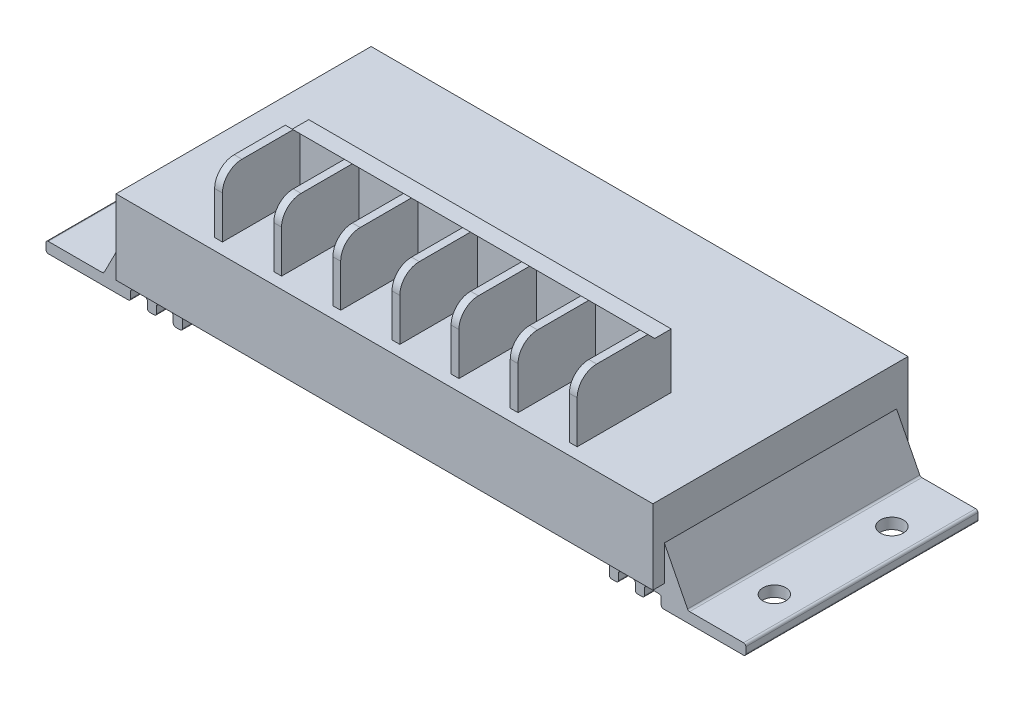
SolidWorks part; units mm, degrees
ref_plane "Front Plane" through (0, 0, 0) normal (0, 0, 1) x (1, 0, 0)
ref_plane "Top Plane" through (0, 0, 0) normal (0, 1, 0) x (1, 0, 0)
ref_plane "Right Plane" through (0, 0, 0) normal (1, 0, 0) x (0, 0, -1)
sketch "Sketch1" plane through (0, 0, 0) normal (0, 1, 0) x (1, 0, 0)
  line L1 (58.5, -27.8) -> (-58.5, -27.8)
  line L2 (58.5, -27.8) -> (58.5, 27.8)
  line L3 (58.5, 27.8) -> (-58.5, 27.8)
  line L4 (-58.5, -27.8) -> (-58.5, 27.8)
  line L5 (58.5, -27.8) -> (-58.5, 27.8) construction
  line L6 (58.5, 27.8) -> (-58.5, -27.8) construction
  point P0 (0, 0)
  dimension "D1" = 117
  dimension "D2" = 55.6
extrude "Boss-Extrude1" add sketch "Sketch1" along normal blind 16.3
sketch "Sketch2" plane through (0, 16.3, 0) normal (0, 1, 0) x (1, 0, 0)
  line L0 (-58.5, -27.8) -> (58.5, -27.8) construction
  line L1 (39.5, -27.8) -> (-39.5, -27.8)
  line L2 (39.5, -27.8) -> (39.5, -4.8)
  line L3 (39.5, -4.8) -> (-39.5, -4.8)
  line L4 (-39.5, -27.8) -> (-39.5, -4.8)
  point P6 (0, -4.8)
  point P8 (-38.8309, -11.3382)
  dimension "D1" = 79
  dimension "D2" = 23
extrude "Boss-Extrude2" add sketch "Sketch2" along normal blind 13.5
sketch "Sketch4" plane through (0, 29.8, 0) normal (0, 1, 0) x (1, 0, 0)
  line L0 (-37.8, -27.8) -> (-37.8, -8.4)
  line L1 (-39.5, -27.8) -> (39.5, -27.8) construction
  line L2 (-37.8, -8.4) -> (-26.6167, -8.4)
  line L3 (-26.6167, -8.4) -> (-26.6167, -27.8)
  line L4 (-37.8, -27.8) -> (-26.6167, -27.8)
  line L5 (-24.9167, -27.8) -> (-24.9167, -8.4)
  line L6 (-24.9167, -8.4) -> (-13.7333, -8.4)
  line L7 (-13.7333, -8.4) -> (-13.7333, -27.8)
  line L8 (-24.9167, -27.8) -> (-13.7333, -27.8)
  line L9 (-12.0333, -27.8) -> (-12.0333, -8.4)
  line L10 (-12.0333, -8.4) -> (-0.85, -8.4)
  line L11 (-0.85, -8.4) -> (-0.85, -27.8)
  line L12 (-12.0333, -27.8) -> (-0.85, -27.8)
  line L13 (0.85, -27.8) -> (0.85, -8.4)
  line L14 (0.85, -8.4) -> (12.0333, -8.4)
  line L15 (12.0333, -8.4) -> (12.0333, -27.8)
  line L16 (0.85, -27.8) -> (12.0333, -27.8)
  line L17 (13.7333, -27.8) -> (13.7333, -8.4)
  line L18 (13.7333, -8.4) -> (24.9167, -8.4)
  line L19 (24.9167, -8.4) -> (24.9167, -27.8)
  line L20 (13.7333, -27.8) -> (24.9167, -27.8)
  line L21 (26.6167, -27.8) -> (26.6167, -8.4)
  line L22 (26.6167, -8.4) -> (37.8, -8.4)
  line L23 (37.8, -8.4) -> (37.8, -27.8)
  line L24 (37.8, -8.4) -> (39.5, -8.4) construction
  line L25 (39.5, -27.8) -> (39.5, -4.8) construction
  line L26 (26.6167, -8.4) -> (24.9167, -8.4) construction
  line L27 (13.7333, -8.4) -> (12.0333, -8.4) construction
  line L28 (0.85, -8.4) -> (-0.85, -8.4) construction
  line L29 (-12.0333, -8.4) -> (-13.7333, -8.4) construction
  line L30 (-24.9167, -8.4) -> (-26.6167, -8.4) construction
  line L31 (-37.8, -8.4) -> (-39.5, -8.4) construction
  line L32 (-39.5, -4.8) -> (-39.5, -27.8) construction
  line L33 (39.5, -4.8) -> (-39.5, -4.8) construction
  line L34 (26.6167, -27.8) -> (37.8, -27.8)
  dimension "D1" = 1.7
  dimension "D2" = 3.6
extrude "Cut-Extrude2" cut sketch "Sketch4" against normal up to surface (13.5 mm away) up to face at (0, 16.3, 8.15)
sketch "Sketch3" plane through (39.5, 0, 0) normal (1, 0, 0) x (0, 0, -1)
  line L0 (-27.8, 16.3) -> (-25.3, 16.3)
  line L1 (-27.8, 16.3) -> (27.8, 16.3) construction
  line L2 (-25.3, 16.3) -> (-25.3, 25.55)
  line L3 (-4.8, 29.8) -> (-4.8, 16.3) construction
  line L5 (-9.9, 29.8) -> (-8.4, 28.3)
  line L6 (-8.4, 28.3) -> (-4.8, 28.3)
  line L7 (-4.8, 28.3) -> (-4.8, 29.8)
  line L9 (-27.8, 29.8) -> (-27.8, 16.3)
  line L10 (-27.8, 29.8) -> (-4.8, 29.8) construction
  line L11 (-21.05, 29.8) -> (-27.8, 29.8)
  line L12 (-9.9, 29.8) -> (-4.8, 29.8)
  line L13 (-27.8, 16.3) -> (-4.8, 16.3) construction
  arc A0 (-25.3, 25.55) -> (-21.05, 29.8) centre (-21.05, 25.55) cw
  point P11 (-11.429, 29.8)
  point P20 (-8.4, 27.0258)
  point P23 (-25.3, 26.0658)
  dimension "D2" = 4.25
  dimension "D1" = 2.5
  dimension "D3" = 3.6
  dimension "D4" = 45
  dimension "D5" = 12
extrude "Cut-Extrude1" cut sketch "Sketch3" against normal up to surface (79 mm away) up to face at (-39.5, 23.05, 16.3)
ref_plane "Plane1" through (0, 0, 25.3) normal (0, 0, 1) x (1, 0, 0)
sketch "Sketch5" plane through (0, 0, 25.3) normal (0, 0, 1) x (1, 0, 0)
  line L0 (-58.5, 7.6556) -> (-63.7, -2.55)
  line L1 (-58.5, 16.3) -> (-58.5, 0) construction
  line L2 (-63.7, -2.55) -> (-76.25, -2.55)
  line L3 (-76.25, -2.55) -> (-76.25, -4.9)
  line L4 (-76.25, -4.9) -> (-57.82, -4.9)
  line L5 (-57.82, -4.9) -> (-57.82, -2.5)
  line L6 (-57.82, -2.5) -> (-54.17, -2.5)
  line L7 (-54.17, -2.5) -> (-54.17, -4.9)
  line L8 (-54.17, -4.9) -> (-52.17, -4.9)
  line L9 (-52.17, -4.9) -> (-52.17, -2.5)
  line L10 (-52.17, -2.5) -> (-48.52, -2.5)
  line L11 (-48.52, -2.5) -> (-48.52, -4.9)
  line L12 (-48.52, -4.9) -> (-46.52, -4.9)
  line L13 (-46.52, -4.9) -> (-46.52, 0)
  line L14 (-58.5, 0) -> (58.5, 0) construction
  line L15 (-46.52, 0) -> (-58.5, 0)
  line L16 (-58.5, 0) -> (-58.5, 7.6556)
  line L17 (0, -28.8398) -> (0, 59.8286) construction
  line L18 (58.5, 0) -> (58.5, 7.6556)
  line L19 (46.52, 0) -> (58.5, 0)
  line L20 (46.52, -4.9) -> (46.52, 0)
  line L21 (48.52, -4.9) -> (46.52, -4.9)
  line L22 (48.52, -2.5) -> (48.52, -4.9)
  line L23 (52.17, -2.5) -> (48.52, -2.5)
  line L24 (52.17, -4.9) -> (52.17, -2.5)
  line L25 (54.17, -4.9) -> (52.17, -4.9)
  line L26 (54.17, -2.5) -> (54.17, -4.9)
  line L27 (57.82, -2.5) -> (54.17, -2.5)
  line L28 (57.82, -4.9) -> (57.82, -2.5)
  line L29 (76.25, -4.9) -> (57.82, -4.9)
  line L30 (76.25, -2.55) -> (76.25, -4.9)
  line L31 (63.7, -2.55) -> (76.25, -2.55)
  line L32 (58.5, 7.6556) -> (63.7, -2.55)
  point P21 (-58.1397, -2.448)
  point P24 (-50.2011, -2.448)
  dimension "D1" = 29.73
  dimension "D2" = 2.35
  dimension "D3" = 12.55
  dimension "D4" = 117
  dimension "D5" = 4.9
  dimension "D6" = 2
  dimension "D7" = 3.65
  dimension "D8" = 2.4
  dimension "D9" = 152.5
extrude "Boss-Extrude3" add sketch "Sketch5" against normal offset from surface (50.6 mm away) 2.5 up to face at (0, 8.15, -27.8)
sketch "Sketch7" plane through (0, -2.55, 0) normal (0, 1, 0) x (1, 0, 0)
  line L0 (-76.25, 25.3) -> (-63.7, 25.3) construction
  line L1 (-105.3743, 0) -> (102.0064, 0) construction
  line L2 (0, 51.5166) -> (0, -54.9347) construction
  circle A0 centre (-69.975, 12.8) radius 2.5
  circle A2 centre (69.975, 12.8) radius 2.5
  circle A3 centre (69.975, -12.8) radius 2.5
  circle A4 centre (-69.975, -12.8) radius 2.5
  point P7 (-69.975, 25.3)
  point P8 (-69.975, 9.0523)
  dimension "D2" = 5
  dimension "D1" = 10
extrude "Cut-Extrude3" cut sketch "Sketch7" against normal through all
fillet "Fillet1" radius 0.5 24 edges at (48.52, -2.5, 0) (54.17, -2.5, 0) (46.52, -4.9, 0) (48.52, -4.9, 0) (52.17, -2.5, 0) (52.17, -4.9, 0) (54.17, -4.9, 0) (57.82, -2.5, 0) (57.82, -4.9, 0) (76.25, -4.9, 0) (76.25, -2.55, 0) (63.7, -2.55, 0) (-46.52, -4.9, 0) (-52.17, -2.5, 0) (-48.52, -4.9, 0) (-48.52, -2.5, 0) (-52.17, -4.9, 0) (-54.17, -4.9, 0) (-54.17, -2.5, 0) (-57.82, -2.5, 0) (-57.82, -4.9, 0) (-76.25, -4.9, 0) (-76.25, -2.55, 0) (-63.7, -2.55, 0)
